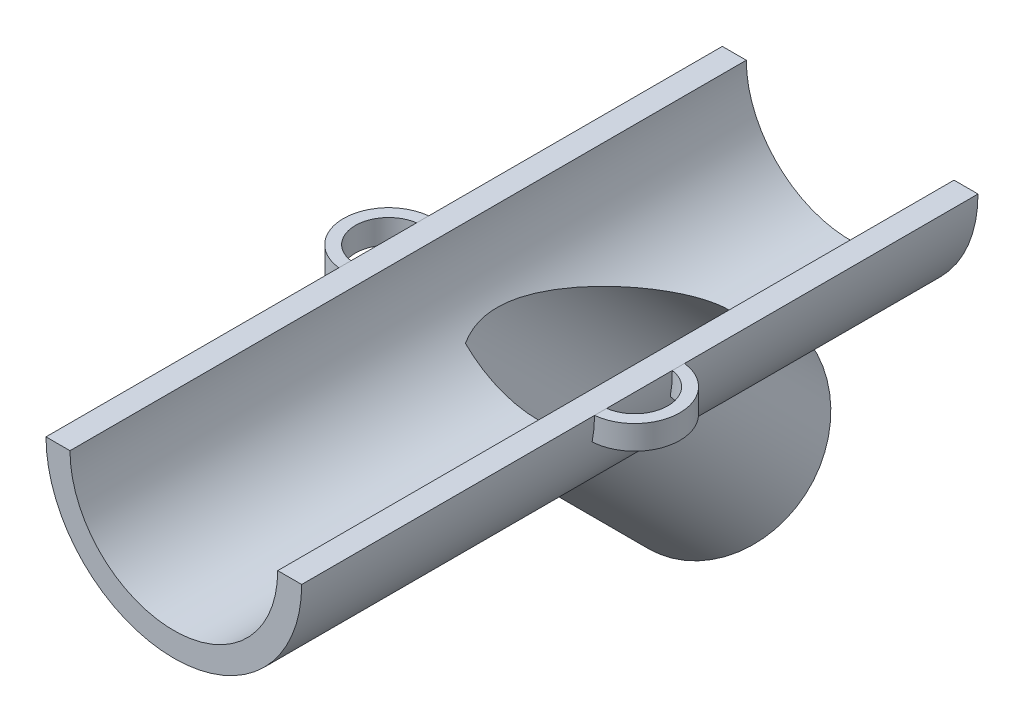
SolidWorks part; units mm, degrees
ref_plane "Front Plane" through (0, 0, 0) normal (0, 0, 1) x (1, 0, 0)
ref_plane "Top Plane" through (0, 0, 0) normal (0, 1, 0) x (1, 0, 0)
ref_plane "Right Plane" through (0, 0, 0) normal (1, 0, 0) x (0, 0, -1)
sketch "Sketch2" plane through (0, 0, 0) normal (0, 0, 1) x (1, 0, 0)
  line L0 (13.54, 0) -> (11, 0)
  line L1 (-11, 0) -> (-13.54, 0)
  arc A0 (-11, 0) -> (11, 0) centre (0, 0) ccw
  arc A1 (-13.54, 0) -> (13.54, 0) centre (0, 0) ccw
  dimension "D1" = 22
  dimension "D2" = 2.54
extrude "Boss-Extrude1" add sketch "Sketch2" along normal blind 76.2
ref_plane "Plane1" through (0, 0, 0) normal (0, 0.7071, 0.7071) x (-1, 0, 0)
sketch "Sketch4" plane through (0, 0, 0) normal (0, 0.7071, 0.7071) x (-1, 0, 0)
  line L5 (-13.54, 0) -> (-11, 0) construction
  line L10 (0, 68.58) -> (0, 0) construction
  circle A0 centre (0, 55.88) radius 10
  dimension "D4" = 20
  dimension "D5" = 55.88
extrude "Boss-Extrude4" add sketch "Sketch4" along normal up to surface (46.7315 mm away)
sketch "Sketch9" plane through (0, 0, 0) normal (0, -0.7071, -0.7071) x (-1, 0, 0)
  circle A0 centre (0, -55.88) radius 8.5
  circle A1 centre (0, -55.88) radius 10 construction
  dimension "D1" = 17
extrude "Cut-Extrude4" cut sketch "Sketch9" against normal through all and the other way through all
sketch "Sketch10" plane through (0, 0, 0) normal (0, 0, -1) x (-1, 0, 0)
  line L0 (13.54, 0) -> (11, 0)
  line L1 (11, 0) -> (13.54, 0) construction
  line L2 (-13.54, 0) -> (-11, 0) construction
  line L3 (-11, 0) -> (-13.54, 0)
  arc A0 (-13.54, 0) -> (13.54, 0) centre (0, 0) ccw construction
  arc A1 (11, 0) -> (-11, 0) centre (0, 0) cw
  arc A2 (-11, 0) -> (11, 0) centre (0, 0) ccw construction
  arc A3 (13.54, 0) -> (-13.54, 0) centre (0, 0) cw
extrude "Cut-Extrude5" cut sketch "Sketch10" against normal blind 43.18
sketch "Sketch11" plane through (0, 0, 76.2) normal (0, 0, 1) x (1, 0, 0)
  line L0 (-11, 0) -> (-13.54, 0) construction
  line L1 (13.54, 0) -> (11, 0) construction
  line L2 (13.54, 0) -> (11, 0)
  line L3 (-11, 0) -> (-13.54, 0)
  arc A0 (11, 0) -> (-11, 0) centre (0, 0) cw
  arc A1 (13.54, 0) -> (-13.54, 0) centre (0, 0) cw
  arc A2 (-13.54, 0) -> (-8.3124, -10.6881) centre (0, 0) ccw construction
extrude "Boss-Extrude5" add sketch "Sketch11" along normal blind 25.4
sketch "Sketch12" plane through (0, 0, 0) normal (0, 1, 0) x (1, 0, 0)
  line L0 (-13.032, -83.82) -> (-13.032, -82.55)
  line L1 (13.032, -74.246) -> (13.032, -75.516)
  line L2 (13.032, -82.55) -> (13.032, -83.82)
  line L3 (13.54, -101.6) -> (13.54, -43.18) construction
  line L4 (13.54, -101.6) -> (11, -101.6) construction
  line L5 (-13.032, -74.246) -> (-13.032, -75.516)
  line L6 (-13.54, -101.6) -> (-13.54, -43.18) construction
  arc A0 (13.032, -74.246) -> (13.032, -83.82) centre (13.032, -79.033) cw
  arc A1 (13.032, -75.516) -> (13.032, -82.55) centre (13.032, -79.033) cw
  arc A2 (-13.032, -82.55) -> (-13.032, -75.516) centre (-13.032, -79.033) cw
  arc A3 (-13.032, -83.82) -> (-13.032, -74.246) centre (-13.032, -79.033) cw
  dimension "D3" = 1.27
  dimension "D1" = 0.508
  dimension "D2" = 17.78
  dimension "D4" = 0.508
extrude "Boss-Extrude6" add sketch "Sketch12" against normal blind 2.54 separate body
sketch "Sketch14" plane through (0, 0, 0) normal (0, -0.7071, -0.7071) x (1, 0, 0)
  circle A0 centre (0, 55.88) radius 10
extrude "Cut-Extrude6" cut sketch "Sketch14" against normal blind 25.4
sketch "Sketch15" plane through (0, 0, 101.6) normal (0, 0, 1) x (1, 0, 0)
  line L0 (-11, 0) -> (-13.54, 0) construction
  line L1 (13.54, 0) -> (11, 0)
  line L2 (-11, 0) -> (-13.54, 0)
  arc A0 (13.54, 0) -> (-13.54, 0) centre (0, 0) cw
  arc A1 (11, 0) -> (-11, 0) centre (0, 0) cw
extrude "Boss-Extrude7" add sketch "Sketch15" along normal blind 13.208
